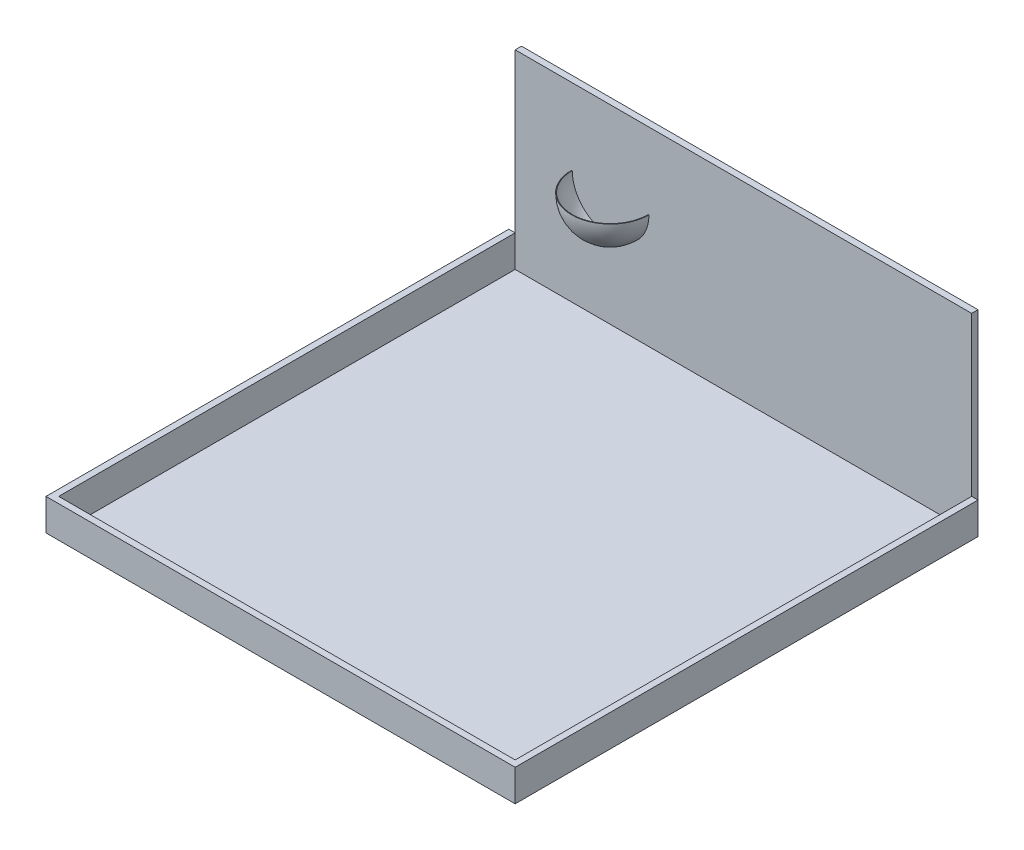
SolidWorks part; units mm, degrees
ref_plane "Front Plane" through (0, 0, 0) normal (0, 0, 1) x (1, 0, 0)
ref_plane "Top Plane" through (0, 0, 0) normal (0, 1, 0) x (1, 0, 0)
ref_plane "Right Plane" through (0, 0, 0) normal (1, 0, 0) x (0, 0, -1)
sketch "Sketch1" plane through (0, 0, 0) normal (0, 1, 0) x (1, 0, 0)
  line L1 (0, 0) -> (1828.8, 0)
  line L2 (0, 0) -> (0, 1828.8)
  line L3 (0, 1828.8) -> (1828.8, 1828.8)
  line L4 (1828.8, 0) -> (1828.8, 1828.8)
  dimension "D1" = 1828.8
  dimension "D2" = 1828.8
extrude "Boss-Extrude1" add sketch "Sketch1" along normal blind 25.4
sketch "Sketch2" plane through (0, 25.4, 0) normal (0, 1, 0) x (1, 0, 0)
  line L0 (914.4, 1828.8) -> (914.4, 0)
  line L1 (1828.8, 1828.8) -> (0, 1828.8) construction
  line L2 (0, 0) -> (1828.8, 0) construction
  line L3 (0, 1219.2) -> (1828.8, 1219.2)
  line L4 (0, 1828.8) -> (0, 0) construction
  line L5 (1828.8, 0) -> (1828.8, 1828.8) construction
  line L6 (0, 609.6) -> (1828.8, 609.6)
  line L7 (381, 1295.4) -> (381, 1143)
  line L8 (1447.8, 1295.4) -> (1447.8, 1143)
  line L9 (1447.8, 685.8) -> (1447.8, 533.4)
  line L10 (381, 685.8) -> (381, 533.4)
  point P20 (381, 1219.2)
  point P23 (381, 609.6)
  dimension "D1" = 609.6
  dimension "D2" = 609.6
  dimension "D3" = 381
  dimension "D4" = 76.2
  dimension "D5" = 2
sketch "Sketch4" plane through (0, 25.4, 0) normal (0, 1, 0) x (1, 0, 0)
  line L1 (0, 1828.8) -> (1828.8, 1828.8)
  line L2 (0, 1828.8) -> (0, 1854.2)
  line L3 (0, 1854.2) -> (1828.8, 1854.2)
  line L4 (1828.8, 1828.8) -> (1828.8, 1854.2)
  point P5 (1828.8, 1828.8)
  dimension "D1" = 25.4
extrude "Boss-Extrude2" add sketch "Sketch4" along normal blind 762 separate body
sketch "Sketch5" plane through (0, 25.4, 0) normal (0, 1, 0) x (1, 0, 0)
  line L1 (0, 1828.8) -> (-25.4, 1828.8)
  line L2 (0, 1828.8) -> (0, 0)
  line L4 (-25.4, 1828.8) -> (-25.4, -25.4)
  line L5 (0, 0) -> (1828.8, 0)
  line L7 (-25.4, -25.4) -> (1854.2, -25.4)
  line L9 (1828.8, 1828.8) -> (1854.2, 1828.8)
  line L10 (1828.8, 1828.8) -> (1828.8, 0)
  line L12 (1854.2, 1828.8) -> (1854.2, -25.4)
  point P7 (0, 0)
  point P13 (1828.8, -1.6886)
  point P14 (0, 0)
  dimension "D1" = 25.4
  dimension "D2" = 25.4
  dimension "D3" = 25.4
extrude "Boss-Extrude3" add sketch "Sketch5" along normal blind 127 separate body
sketch "Sketch6" plane through (0, 0, -1828.8) normal (0, 0, 1) x (1, 0, 0)
  line L1 (0, 25.4) -> (1828.8, 25.4) construction
  line L2 (0, 787.4) -> (0, 25.4) construction
  line L3 (226.06, 482.6) -> (228.6, 482.6)
  line L4 (381, 330.2) -> (381, 327.66)
  arc A0 (228.6, 482.6) -> (381, 330.2) centre (381, 482.6) ccw
  arc A1 (226.06, 482.6) -> (381, 327.66) centre (381, 482.6) ccw
  dimension "D1" = 152.4
  dimension "D2" = 457.2
  dimension "D3" = 381
  dimension "D4" = 152.4
  dimension "D5" = 0
  dimension "D6" = 2.54
revolve "Revolve1" add sketch "Sketch6" angle 180 about L4
equation "\"D3@Sketch2\"=15"
